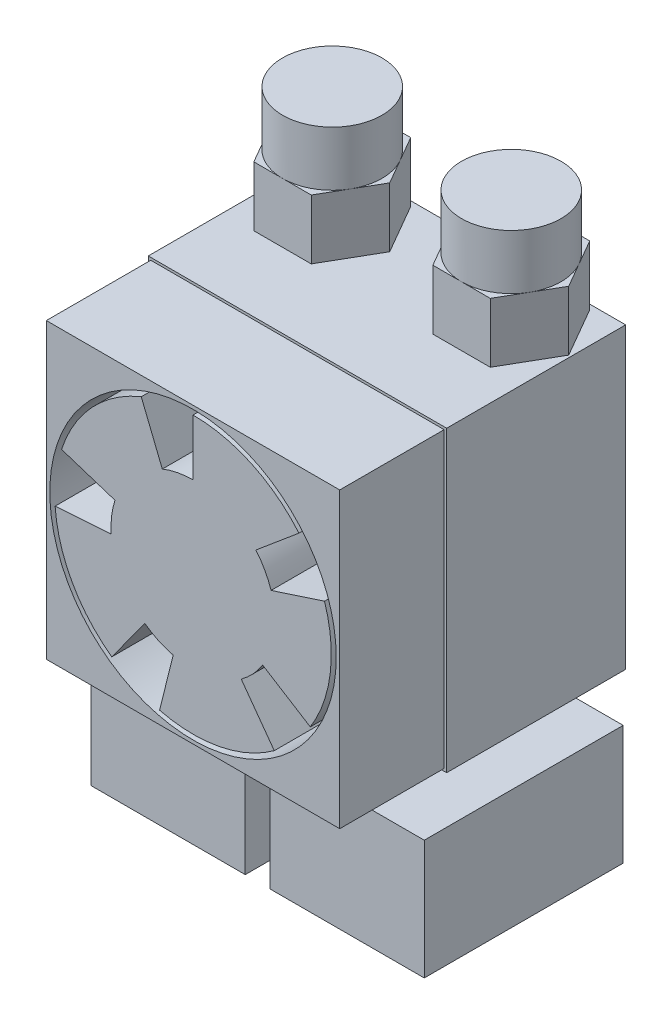
SolidWorks part; units mm, degrees
ref_plane "Plano frontal" through (0, 0, 0) normal (0, 0, 1) x (1, 0, 0)
ref_plane "Plano superior" through (0, 0, 0) normal (0, 1, 0) x (1, 0, 0)
ref_plane "Plano direito" through (0, 0, 0) normal (1, 0, 0) x (0, 0, -1)
sketch "Esboço1" plane through (0, 0, 0) normal (0, 0, 1) x (1, 0, 0)
  line L1 (-15, 15) -> (15, 15)
  line L2 (-15, 15) -> (-15, -15)
  line L3 (-15, -15) -> (15, -15)
  line L4 (15, 15) -> (15, -15)
  line L5 (-15, 15) -> (15, -15) construction
  line L6 (-15, -15) -> (15, 15) construction
  point P0 (0, 0)
  dimension "D1" = 30
  dimension "D2" = 30
extrude "Ressalto-extrusão1" add sketch "Esboço1" along normal blind 28.5
sketch "Esboço2" plane through (0, 0, 0) normal (0, 0, -1) x (-1, 0, 0)
  line L0 (-15, 15) -> (15, 15) construction
  line L1 (0, 0) -> (0, 11.5425) construction
  circle A0 centre (4.5, 5) radius 1.6
  circle A1 centre (-4.5, 5) radius 1.6
  circle A2 centre (0, -4.8) radius 1.6
  dimension "D4" = 3.2
  dimension "D1" = 10
  dimension "D2" = 9
  dimension "D3" = 9.8
extrude "Corte-extrusão1" cut sketch "Esboço2" against normal blind 5
sketch "Esboço3" plane through (0, -15, 0) normal (0, -1, 0) x (1, 0, 0)
  line L0 (0, 0) -> (0, 10.5466) construction
  line L1 (-15, 0) -> (15, 0) construction
  circle A0 centre (-9, 5.5) radius 2.25
  circle A1 centre (9, 5.5) radius 2.25
  dimension "D3" = 4.5
  dimension "D1" = 18
  dimension "D2" = 5.5
extrude "Ressalto-extrusão2" add sketch "Esboço3" along normal blind 3
sketch "Esboço4" plane through (0, -18, 0) normal (0, -1, 0) x (1, 0, 0)
  line L0 (0, 0) -> (0, 24.4344) construction
  line L1 (-1.25, 22) -> (-16.75, 22)
  line L2 (-1.25, 22) -> (-1.25, 2)
  line L3 (-1.25, 2) -> (-16.75, 2)
  line L4 (-16.75, 22) -> (-16.75, 2)
  line L5 (-1.25, 22) -> (-16.75, 2) construction
  line L6 (-1.25, 2) -> (-16.75, 22) construction
  line L7 (-15, 0) -> (15, 0) construction
  line L8 (1.25, 2) -> (16.75, 22) construction
  line L9 (1.25, 22) -> (16.75, 2) construction
  line L10 (16.75, 22) -> (16.75, 2)
  line L11 (1.25, 2) -> (16.75, 2)
  line L12 (1.25, 22) -> (1.25, 2)
  line L13 (1.25, 22) -> (16.75, 22)
  point P0 (-9, 12)
  point P13 (9, 12)
  point P14 (9, 5.5)
  point P17 (9, 2)
  dimension "D1" = 20
  dimension "D2" = 15.5
  dimension "D3" = 2
extrude "Ressalto-extrusão3" add sketch "Esboço4" along normal blind 12
sketch "Esboço5" plane through (0, -30, 0) normal (0, -1, 0) x (1, 0, 0)
  circle A0 centre (9, 5.5) radius 2.25 construction
  circle A1 centre (9, 5.5) radius 2.25
  circle A2 centre (-9, 5.5) radius 2.25 construction
  circle A3 centre (-9, 5.5) radius 2.25
extrude "Ressalto-extrusão4" add sketch "Esboço5" along normal blind 5 draft 22
sketch "Esboço6" plane through (0, 0, 28.5) normal (0, 0, 1) x (1, 0, 0)
  line L0 (6.3199, 5.303) -> (10.648, 8.9347)
  line L1 (-14.75, 14.75) -> (14.75, 14.75)
  line L2 (-14.75, 14.75) -> (-14.75, -14.75)
  line L3 (-14.75, -14.75) -> (14.75, -14.75)
  line L4 (14.75, 14.75) -> (14.75, -14.75)
  line L5 (-14.75, 14.75) -> (14.75, -14.75) construction
  line L6 (-14.75, -14.75) -> (14.75, 14.75) construction
  line L7 (7.8462, 2.5494) -> (13.2197, 4.2953)
  line L10 (4.8492, -6.6744) -> (8.1702, -11.2453)
  line L11 (6.9964, -4.3718) -> (11.7879, -7.3659)
  line L12 (-4.8492, -6.6744) -> (-8.1702, -11.2453)
  line L13 (-1.9959, -8.0049) -> (-3.3627, -13.4871)
  line L14 (-7.8462, 2.5494) -> (-13.2197, 4.2953)
  line L15 (-8.2299, -0.5755) -> (-13.8661, -0.9696)
  line L16 (0, 8.25) -> (0, 13.9)
  line L17 (-3.0905, 7.6493) -> (-5.207, 12.8879)
  line L21 (15, -15) -> (15, 15)
  line L22 (15, 15) -> (-15, 15)
  line L23 (-15, 15) -> (-15, -15)
  line L24 (-15, -15) -> (15, -15)
  line L25 (15, -15) -> (15, 15)
  line L26 (15, 15) -> (-15, 15)
  line L27 (-15, 15) -> (-15, -15)
  line L28 (-15, -15) -> (15, -15)
  arc A0 (-5.207, 12.8879) -> (-13.2197, 4.2953) centre (0, 0) ccw
  arc A2 (7.8462, 2.5494) -> (6.3199, 5.303) centre (0, 0) ccw
  arc A3 (4.8492, -6.6744) -> (6.9964, -4.3718) centre (0, 0) ccw
  arc A4 (-4.8492, -6.6744) -> (-1.9959, -8.0049) centre (0, 0) ccw
  arc A5 (0, 8.25) -> (-3.0905, 7.6493) centre (0, 0) ccw
  circle A6 centre (0, 0) radius 14.4
  arc A7 (-13.8661, -0.9696) -> (-8.1702, -11.2453) centre (0, 0) ccw
  arc A8 (-3.3627, -13.4871) -> (8.1702, -11.2453) centre (0, 0) ccw
  arc A9 (11.7879, -7.3659) -> (13.2197, 4.2953) centre (0, 0) ccw
  arc A10 (10.648, 8.9347) -> (0, 13.9) centre (0, 0) ccw
  arc A11 (-7.8462, 2.5494) -> (-8.2299, -0.5755) centre (0, 0) ccw
  point P0 (0, 0)
  point P33 (0, 0)
  line M15 (15, -15) -> (15, 15)
  line M16 (15, 15) -> (-15, 15)
  line M17 (-15, 15) -> (-15, -15)
  line M18 (-15, -15) -> (15, -15)
  dimension "D2" = 27.8
  dimension "D3" = 8.25
  dimension "D7" = 0.5
  dimension "D1" = 29.5
  dimension "D5" = 50
  dimension "D8" = 0
  dimension "D4" = 5
extrude "Corte-extrusão2" cut sketch "Esboço6" against normal blind 10.5 contours L1 L4 L3 L2 M18 M15 M16 M17 | A6 A11 L14 A0 L17 A5 L16 A10 L0 A2 L7 A9 L11 A3 L10 A8 L13 A4 L12 A7 L15
sketch "Esboço9" plane through (0, 15, 0) normal (0, 1, 0) x (1, 0, 0)
  line L1 (14.7735, -5.5) -> (11.8868, -0.5)
  line L2 (11.8868, -0.5) -> (6.1132, -0.5)
  line L3 (6.1132, -0.5) -> (3.2265, -5.5)
  line L4 (3.2265, -5.5) -> (6.1132, -10.5)
  line L5 (6.1132, -10.5) -> (11.8868, -10.5)
  line L6 (11.8868, -10.5) -> (14.7735, -5.5)
  line L7 (-3.2265, -5.5) -> (-6.1132, -0.5)
  line L8 (-6.1132, -0.5) -> (-11.8868, -0.5)
  line L9 (-11.8868, -0.5) -> (-14.7735, -5.5)
  line L10 (-14.7735, -5.5) -> (-11.8868, -10.5)
  line L11 (-11.8868, -10.5) -> (-6.1132, -10.5)
  line L12 (-6.1132, -10.5) -> (-3.2265, -5.5)
  circle A0 centre (-9, -5.5) radius 2.25 construction
  circle A1 centre (9, -5.5) radius 2.25 construction
  circle A2 centre (-9, -5.5) radius 2.25 construction
  circle A3 centre (9, -5.5) radius 2.25 construction
  circle A4 centre (9, -5.5) radius 5 construction
  circle A5 centre (-9, -5.5) radius 5 construction
  dimension "D1" = 10
extrude "Ressalto-extrusão5" add sketch "Esboço9" along normal blind 6
sketch "Esboço10" plane through (0, 21, 0) normal (0, 1, 0) x (1, 0, 0)
  line L0 (11.8868, -0.5) -> (6.1132, -0.5) construction
  line L1 (-6.1132, -0.5) -> (-11.8868, -0.5) construction
  circle A0 centre (-9, -5.5) radius 5
  circle A1 centre (9, -5.5) radius 5
  point P4 (0, 0)
  point P5 (10.2163, -6.5636)
  point P8 (9, -0.5)
  point P10 (0, 0)
  point P13 (-9, -0.5)
  dimension "D1" = 10
extrude "Ressalto-extrusão6" add sketch "Esboço10" along normal offset from surface (5.5 mm away) 11.5 up to face at (9, 15, 5.5) offset beyond the face yes
